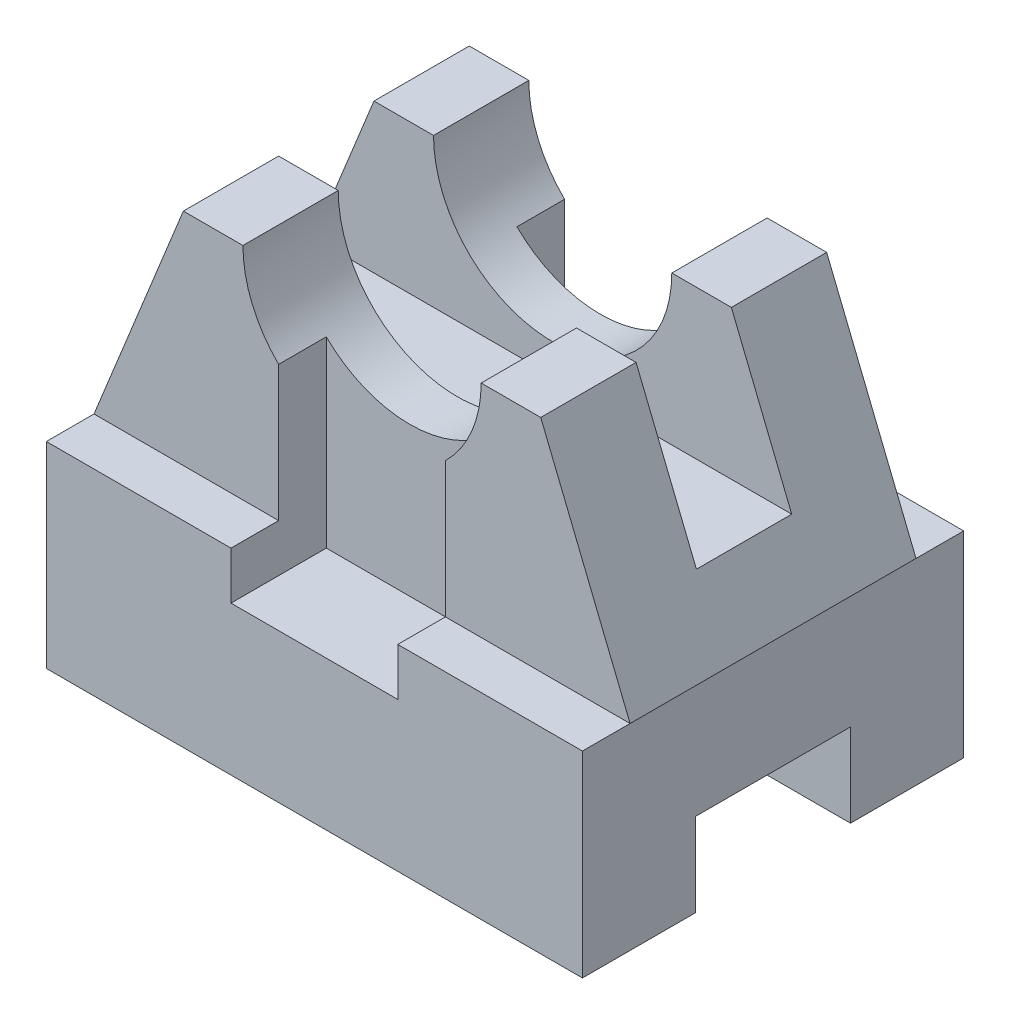
SolidWorks part; units mm, degrees
ref_plane "Front Plane" through (0, 0, 0) normal (0, 0, 1) x (1, 0, 0)
ref_plane "Top Plane" through (0, 0, 0) normal (0, 1, 0) x (1, 0, 0)
ref_plane "Right Plane" through (0, 0, 0) normal (1, 0, 0) x (0, 0, -1)
sketch "Sketch1" plane through (0, 0, 0) normal (0, 1, 0) x (1, 0, 0)
  line L0 (-45.8721, 0) -> (44.1279, 0)
  line L1 (-45.8721, 0) -> (-45.8721, 64)
  line L2 (44.1279, 0) -> (44.1279, 64)
  line L3 (-45.8721, 64) -> (44.1279, 64)
  dimension "D1" = 90
  dimension "D2" = 64
extrude "Boss-Extrude1" add sketch "Sketch1" along normal blind 70
sketch "Sketch2" plane through (-45.8721, 0, 0) normal (-1, 0, 0) x (0, 0, 1)
  line L0 (-64, 0) -> (0, 0) construction
  line L1 (-45, 0) -> (-19, 0)
  line L2 (-45, 0) -> (-45, 14)
  line L3 (-45, 14) -> (-19, 14)
  line L4 (-19, 0) -> (-19, 14)
  line L5 (-64, 70) -> (-64, 0) construction
  line L6 (0, 70) -> (0, 0) construction
  dimension "D1" = 26
  dimension "D2" = 14
  dimension "D3" = 19
  dimension "D4" = 19
extrude "Cut-Extrude1" cut sketch "Sketch2" against normal blind 90
sketch "Sketch3" plane through (-45.8721, 0, 0) normal (-1, 0, 0) x (0, 0, 1)
  line L0 (0, 33) -> (-8, 33)
  line L1 (0, 70) -> (0, 0) construction
  line L2 (-8, 33) -> (-8, 70)
  line L3 (-64, 70) -> (0, 70) construction
  dimension "D1" = 8
  dimension "D2" = 37
extrude "Cut-Extrude3" cut sketch "Sketch3" against normal through all and the other way through all flip side to cut
ref_plane "Plane1" through (0, 0, -32) normal (0, 0, -1) x (-1, 0, 0)
mirror "Mirror2" about plane through (0, 0, -32) normal (0, 0, -1) of "Cut-Extrude3"
sketch "Sketch7" plane through (0, 0, -8) normal (0, 0, 1) x (1, 0, 0)
  line L0 (-45.8721, 70) -> (44.1279, 70) construction
  circle A0 centre (-0.8721, 70) radius 20
extrude "Cut-Extrude4" cut sketch "Sketch7" against normal blind 48
sketch "Sketch8" plane through (0, 0, -8) normal (0, 0, 1) x (1, 0, 0)
  line L0 (-45.8721, 33) -> (-30.8721, 70)
  line L1 (-45.8721, 70) -> (-20.8721, 70) construction
  dimension "D1" = 15
extrude "Cut-Extrude5" cut sketch "Sketch8" against normal through all and the other way through all
ref_plane "Plane2" through (-0.8721, 0, 0) normal (1, 0, 0) x (0, 0, -1)
mirror "Mirror3" about plane through (-0.8721, 0, 0) normal (1, 0, 0) of "Cut-Extrude5"
ref_plane "Plane3" through (0, 70, 0) normal (0, 1, 0) x (1, 0, 0)
sketch "Sketch11" plane through (0, 70, 0) normal (0, 1, 0) x (1, 0, 0)
  line L0 (44.1279, 8) -> (44.1279, 56) construction
  line L1 (44.1279, 40) -> (-45.8721, 40)
  line L2 (44.1279, 40) -> (44.1279, 24)
  line L3 (44.1279, 24) -> (-45.8721, 24)
  line L4 (-45.8721, 40) -> (-45.8721, 24)
  line L5 (-45.8721, 8) -> (-45.8721, 56) construction
  line L6 (-45.8721, 56) -> (44.1279, 56) construction
  line L7 (-30.8721, 8) -> (-20.8721, 8) construction
  dimension "D1" = 16
  dimension "D2" = 16
extrude "Cut-Extrude7" cut sketch "Sketch11" against normal blind 25
ref_plane "Plane6" through (0, 70, 0) normal (0, -1, 0) x (-1, 0, 0)
sketch "Sketch13" plane through (0, 70, 0) normal (0, -1, 0) x (-1, 0, 0)
  line L0 (45.8721, 0) -> (-44.1279, 0) construction
  line L1 (14.8721, 0) -> (-13.1279, 0)
  line L2 (14.8721, 0) -> (14.8721, 16)
  line L3 (14.8721, 16) -> (-13.1279, 16)
  line L4 (-13.1279, 0) -> (-13.1279, 16)
  line L5 (45.8721, 0) -> (45.8721, 8) construction
  line L6 (-44.1279, 8) -> (-44.1279, 0) construction
  point P8 (-44.1279, 4)
  dimension "D1" = 31
  dimension "D2" = 31
  dimension "D3" = 16
extrude "Cut-Extrude8" cut sketch "Sketch13" along normal blind 45
mirror "Mirror4" about plane through (0, 0, -32) normal (0, 0, -1) of "Cut-Extrude8"
